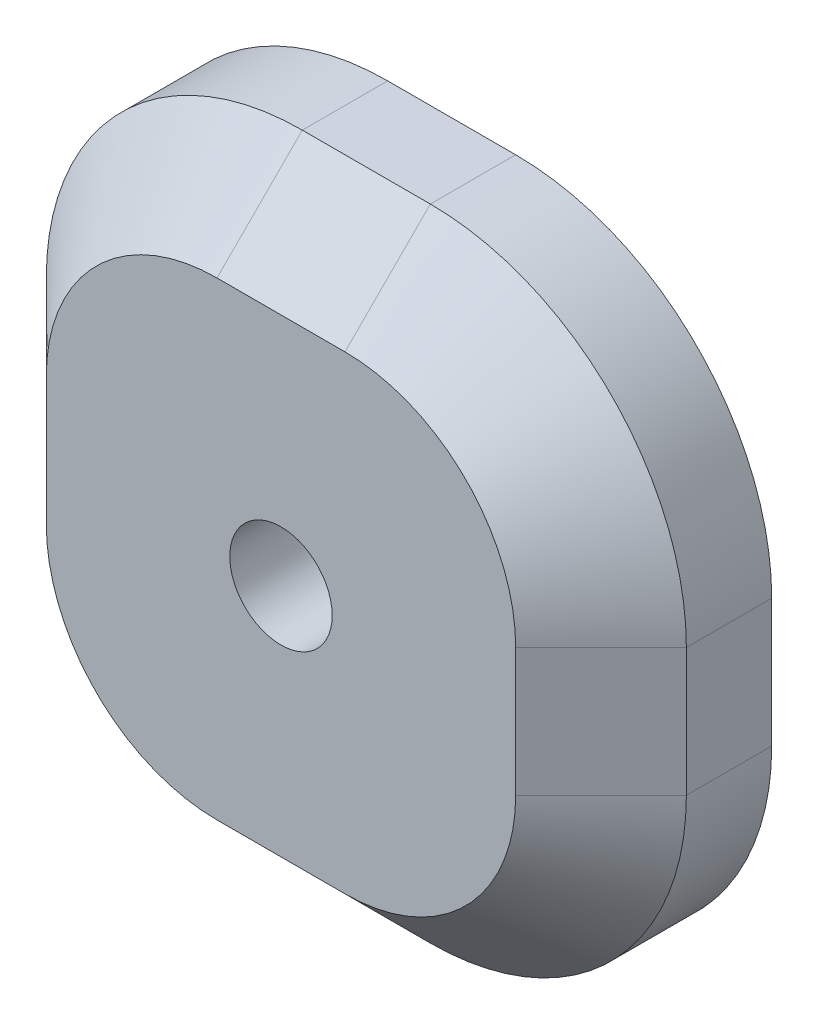
SolidWorks part; units mm, degrees
ref_plane "Alzado" through (0, 0, 0) normal (0, 0, 1) x (1, 0, 0)
ref_plane "Planta" through (0, 0, 0) normal (0, 1, 0) x (1, 0, 0)
ref_plane "Vista lateral" through (0, 0, 0) normal (1, 0, 0) x (0, 0, -1)
sketch "Croquis1" plane through (0, 0, 0) normal (0, 0, 1) x (1, 0, 0)
  line L1 (-7.5, 37.5) -> (7.5, 37.5)
  line L2 (-37.5, 7.5) -> (-37.5, -7.5)
  line L3 (-7.5, -37.5) -> (7.5, -37.5)
  line L4 (37.5, 7.5) -> (37.5, -7.5)
  line L5 (-37.5, 37.5) -> (37.5, -37.5) construction
  line L6 (-37.5, -37.5) -> (37.5, 37.5) construction
  arc A0 (-37.5, -7.5) -> (-7.5, -37.5) centre (-7.5, -7.5) ccw
  arc A1 (7.5, -37.5) -> (37.5, -7.5) centre (7.5, -7.5) ccw
  arc A2 (7.5, 37.5) -> (37.5, 7.5) centre (7.5, 7.5) cw
  arc A3 (-7.5, 37.5) -> (-37.5, 7.5) centre (-7.5, 7.5) ccw
  point P0 (0, 0)
  dimension "D3" = 30
  dimension "D1" = 75
  dimension "D2" = 75
extrude "Saliente-Extruir3" add sketch "Croquis1" along normal blind 20
chamfer "Chaflán1" distance 10 angle 45 8 edges at (-37.5, 0, 20) (-28.7132, 28.7132, 20) (0, 37.5, 20) (28.7132, 28.7132, 20) (37.5, 0, 20) (28.7132, -28.7132, 20) (-28.7132, -28.7132, 20) (0, -37.5, 20)
sketch "Croquis5" [suppressed] plane through (0, 0, 20) normal (0, 0, 1) x (1, 0, 0)
  line L1 (-12.5, 12.5) -> (12.5, 12.5)
  line L2 (-12.5, 12.5) -> (-12.5, -12.5)
  line L3 (-12.5, -12.5) -> (12.5, -12.5)
  line L4 (12.5, 12.5) -> (12.5, -12.5)
  line L5 (-12.5, 12.5) -> (12.5, -12.5) construction
  line L6 (-12.5, -12.5) -> (12.5, 12.5) construction
  point P0 (0, 0)
  dimension "D1" = 0
sketch "Croquis6" plane through (0, 0, 20) normal (0, 0, 1) x (1, 0, 0)
  line L1 (-12.5, 12.5) -> (12.5, 12.5)
  line L2 (-12.5, 12.5) -> (-12.5, -12.5)
  line L3 (-12.5, -12.5) -> (12.5, -12.5)
  line L4 (12.5, 12.5) -> (12.5, -12.5)
  line L5 (-12.5, 12.5) -> (12.5, -12.5) construction
  line L6 (-12.5, -12.5) -> (12.5, 12.5) construction
  point P0 (0, 0)
  dimension "D1" = 25
hole_wizard "Taladro1" [suppressed] positions "Croquis7" profile "Croquis8" legacy
sketch "Croquis7" [suppressed] plane through (0, 0, 20) normal (0, 0, 1) x (1, 0, 0)
  point P0 (-12.5, 12.5)
  point P3 (-12.5, -12.5)
  point P6 (12.5, -12.5)
  point P9 (12.5, 12.5)
sketch "Croquis8" plane through (-12.5, 12.5, 20) normal (1, 0, 0) x (0, -1, 0)
  line L0 (0, 0) -> (0, 13.6052)
  line L1 (0, 13.6052) -> (6, 10)
  line L2 (6, 10) -> (6, 0)
  line L4 (6, 0) -> (0, 0)
  line L6 (0, 13.6052) -> (-6, 10) construction
  line L7 (0, -4.2442) -> (0, 117.3081) construction
  dimension "Diámetro" = 12
  dimension "Profundidad" = 10
  dimension "Ángulo de perforado" = 118
hole_wizard "Taladro2" positions "Croquis9" profile "Croquis10" legacy
sketch "Croquis9" plane through (0, 0, 0) normal (0, 0, -1) x (-1, 0, 0)
  point P0 (-12.5, 12.5)
  point P3 (-12.5, -12.5)
  point P6 (12.5, -12.5)
  point P9 (12.5, 12.5)
sketch "Croquis10" plane through (12.5, 12.5, 0) normal (1, 0, 0) x (0, 1, 0)
  line L0 (0, 0) -> (0, 13.6052)
  line L1 (0, 13.6052) -> (6, 10)
  line L2 (6, 10) -> (6, 0)
  line L4 (6, 0) -> (0, 0)
  line L6 (0, 13.6052) -> (-6, 10) construction
  line L7 (0, -4.2442) -> (0, 117.3081) construction
  dimension "Diámetro" = 12
  dimension "Profundidad" = 10
  dimension "Ángulo de perforado" = 118
hole_wizard "Taladro3" positions "Croquis12" profile "Croquis13" legacy
sketch "Croquis12" plane through (0, 0, 20) normal (0, 0, 1) x (1, 0, 0)
  point P0 (0, 0)
sketch "Croquis13" plane through (0, 0, 20) normal (1, 0, 0) x (0, -1, 0)
  line L0 (0, 0) -> (0, 13.6052)
  line L1 (0, 13.6052) -> (6, 10)
  line L2 (6, 10) -> (6, 0)
  line L4 (6, 0) -> (0, 0)
  line L6 (0, 13.6052) -> (-6, 10) construction
  line L7 (0, -4.2442) -> (0, 117.3081) construction
  dimension "Diámetro" = 12
  dimension "Profundidad" = 10
  dimension "Ángulo de perforado" = 118
equation "\"A\" = 75"
equation "\"B\" = 0"
equation "\"C\" = 25"
equation "\"D\"= 20"
equation "\"D1@Croquis1\"=\"A\""
equation "\"D2@Croquis1\"=\"A\""
equation "\"D1@Saliente-Extruir3\"=\"D\""
equation "\"D1@Croquis5\"=\"B\""
equation "\"D1@Croquis6\"=\"C\""
